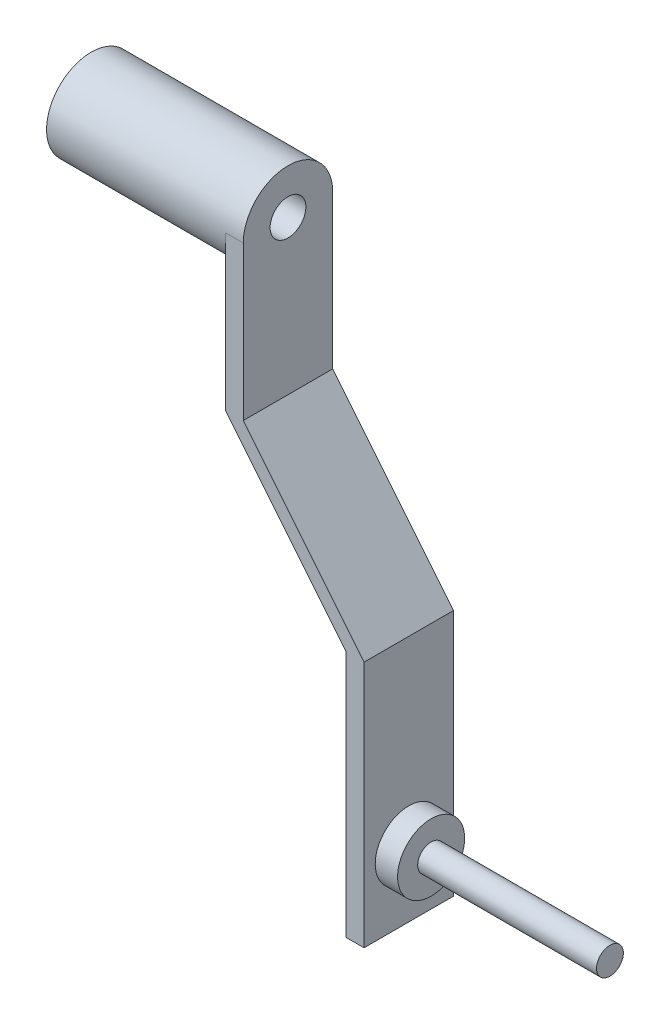
SolidWorks part; units mm, degrees
ref_plane "Front Plane" through (0, 0, 0) normal (0, 0, 1) x (1, 0, 0)
ref_plane "Top Plane" through (0, 0, 0) normal (0, 1, 0) x (1, 0, 0)
ref_plane "Right Plane" through (0, 0, 0) normal (1, 0, 0) x (0, 0, -1)
sketch "Sketch1" plane through (0, 0, 0) normal (1, 0, 0) x (0, 0, -1)
  circle A0 centre (0, 0) radius 5
  dimension "D1" = 10
extrude "Boss-Extrude1" add sketch "Sketch1" along normal blind 20
sketch "Sketch2" plane through (20, 0, 0) normal (1, 0, 0) x (0, 0, -1)
  line L0 (-5, 0) -> (-5, -17.1852)
  line L1 (-5, -17.1852) -> (5, -17.1852)
  line L2 (5, -17.1852) -> (5, 0)
  circle A0 centre (0, 0) radius 5 construction
  arc A1 (5, 0) -> (-5, 0) centre (0, 0) ccw
extrude "Boss-Extrude2" add sketch "Sketch2" along normal blind 2
sketch "Sketch3" plane through (22, 0, 0) normal (1, 0, 0) x (0, 0, -1)
  circle A0 centre (0, 0) radius 2
  dimension "D1" = 4
extrude "Cut-Extrude1" cut sketch "Sketch3" against normal through all
sketch "Sketch4" plane through (0, 0, 0) normal (0, 0, 1) x (1, 0, 0)
  line L0 (20, -17.1852) -> (33.5069, -33.8342)
  line L2 (20, -17.1852) -> (22, -17.1852)
  line L3 (33.5069, -33.8342) -> (35.5069, -33.8342)
  line L4 (22, -17.1852) -> (35.5069, -33.8342)
extrude "Boss-Extrude3" add sketch "Sketch4" along normal mid plane 10
sketch "Sketch5" plane through (0, 0, 0) normal (0, 0, 1) x (1, 0, 0)
  line L1 (33.5069, -33.8342) -> (35.5069, -33.8342)
  line L2 (33.5069, -33.8342) -> (33.5069, -61.5014)
  line L3 (33.5069, -61.5014) -> (35.5069, -61.5014)
  line L4 (35.5069, -33.8342) -> (35.5069, -61.5014)
extrude "Boss-Extrude4" add sketch "Sketch5" along normal mid plane 10
sketch "Sketch6" plane through (35.5069, 0, 0) normal (1, 0, 0) x (0, 0, -1)
  line L0 (5, -61.5014) -> (5, -33.8342) construction
  line L1 (-5, -61.5014) -> (5, -61.5014) construction
  circle A0 centre (0, -54.0014) radius 3.75
  dimension "D1" = 7.5
  dimension "D2" = 5
  dimension "D3" = 7.5
extrude "Boss-Extrude5" add sketch "Sketch6" along normal blind 2.5
sketch "Sketch7" plane through (38.0069, 0, 0) normal (1, 0, 0) x (0, 0, -1)
  circle A0 centre (0, -54.0014) radius 1.5
  dimension "D1" = 3
extrude "Boss-Extrude6" add sketch "Sketch7" along normal blind 20
